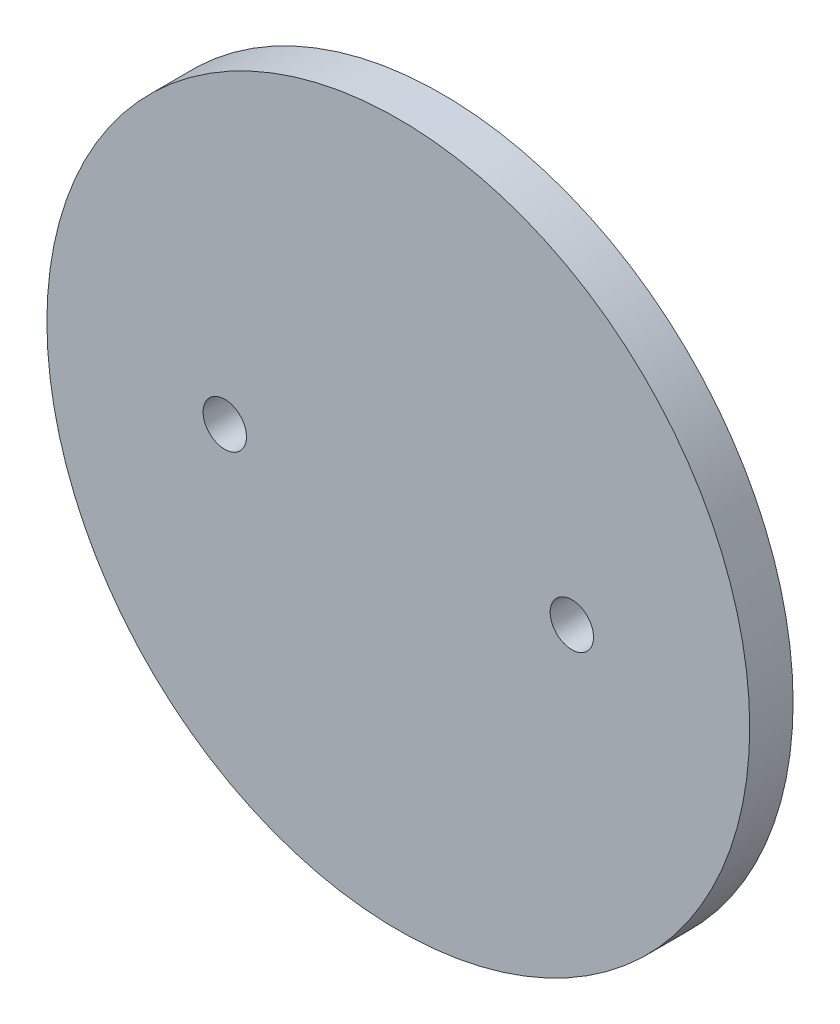
SolidWorks part; units mm, degrees
ref_plane "Front Plane" through (0, 0, 0) normal (0, 0, 1) x (1, 0, 0)
ref_plane "Top Plane" through (0, 0, 0) normal (0, 1, 0) x (1, 0, 0)
ref_plane "Right Plane" through (0, 0, 0) normal (1, 0, 0) x (0, 0, -1)
sketch "Sketch1" plane through (0, 0, 0) normal (0, 0, 1) x (1, 0, 0)
  circle A0 centre (0, 0) radius 20.575
extrude "Boss-Extrude1" add sketch "Sketch1" along normal blind 2.54
sketch "Sketch2" plane through (0, 0, 2.54) normal (0, 0, 1) x (1, 0, 0)
  line L0 (-20.575, 0) -> (20.575, 0)
  circle A0 centre (0, 0) radius 20.575 construction
  circle A1 centre (-10.16, 0) radius 1.27
  circle A2 centre (10.16, 0) radius 1.27
  point P7 (0, 0)
  dimension "D1" = 10.16
  dimension "D2" = 10.16
extrude "Cut-Extrude1" cut sketch "Sketch2" against normal through all contours L0 A1 | L0 A1 | L0 A2 | L0 A2
